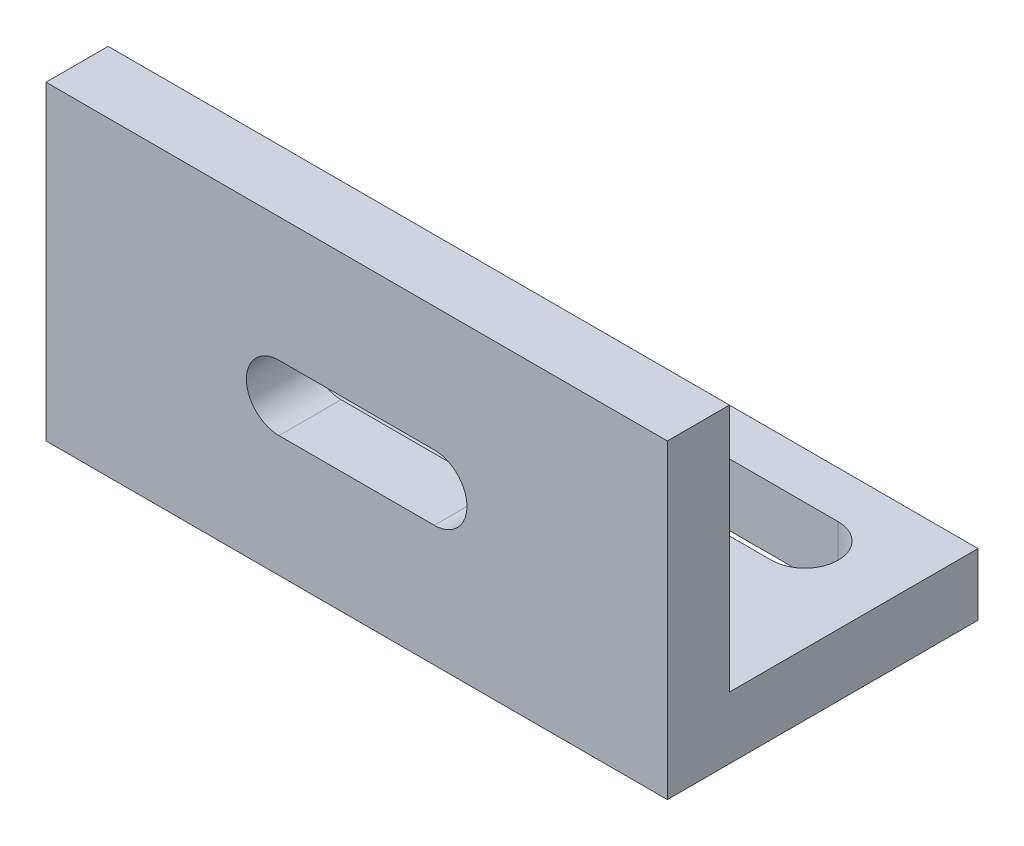
SolidWorks part; units mm, degrees
ref_plane "Front Plane" through (0, 0, 0) normal (0, 0, 1) x (1, 0, 0)
ref_plane "Top Plane" through (0, 0, 0) normal (0, 1, 0) x (1, 0, 0)
ref_plane "Right Plane" through (0, 0, 0) normal (1, 0, 0) x (0, 0, -1)
sketch "Sketch1" plane through (0, 0, 0) normal (0, 1, 0) x (1, 0, 0)
  line L1 (-49.2593, 12.8889) -> (-9.2593, 12.8889)
  line L2 (-49.2593, 12.8889) -> (-49.2593, -7.1111)
  line L4 (-9.2593, 12.8889) -> (-9.2593, -7.1111)
  line L5 (-49.2593, 12.8889) -> (-9.2593, -7.1111) construction
  line L6 (-49.2593, -7.1111) -> (-9.2593, 12.8889) construction
  line L13 (-49.2593, -7.1111) -> (-9.2593, -7.1111)
  line L14 (-49.2593, -7.1111) -> (-49.2593, -3.073)
  line L16 (-9.2593, -7.1111) -> (-9.2593, -3.073)
  point P4 (-29.2593, 2.8889)
  dimension "D1" = 40
  dimension "D2" = 20
extrude "Boss-Extrude1" add sketch "Sketch1" along normal blind 4 contours L2 L13 L4 L1
sketch "Sketch5" plane through (0, 4, 0) normal (0, 1, 0) x (1, 0, 0)
  line L0 (-9.2593, 12.8889) -> (-9.2593, -7.1111) construction
  line L1 (-49.2593, -7.1111) -> (-9.2593, -7.1111)
  line L2 (-49.2593, -7.1111) -> (-49.2593, -3.1111)
  line L3 (-49.2593, -3.1111) -> (-9.2593, -3.1111)
  line L4 (-9.2593, -7.1111) -> (-9.2593, -3.1111)
  line L5 (-49.2593, -7.1111) -> (-9.2593, -3.1111) construction
  line L6 (-49.2593, -3.1111) -> (-9.2593, -7.1111) construction
  point P4 (-29.2593, -5.1111)
  dimension "D1" = 4
extrude "Boss-Extrude2" add sketch "Sketch5" along normal blind 16
sketch "Sketch7" plane through (0, 4, 0) normal (0, 1, 0) x (1, 0, 0)
  line L0 (-49.2593, 12.8889) -> (-9.2593, 12.8889) construction
  line L4 (-15.2593, 7.7389) -> (-43.2593, 7.7389) construction
  line L7 (-15.2593, 5.5889) -> (-43.2593, 5.5889)
  line L8 (-15.2593, 9.8889) -> (-43.2593, 9.8889)
  line L9 (-9.2593, 12.8889) -> (-9.2593, -3.1111) construction
  line L10 (-49.2593, 12.8889) -> (-49.2593, -3.1111) construction
  arc A2 (-15.2593, 5.5889) -> (-15.2593, 9.8889) centre (-15.2593, 7.7389) ccw
  arc A3 (-43.2593, 9.8889) -> (-43.2593, 5.5889) centre (-43.2593, 7.7389) ccw
  point P0 (-29.7561, 8.586)
  point P4 (-29.2593, 12.8889)
  point P8 (-29.2593, 7.7389)
  dimension "D1" = 6
  dimension "D2" = 6
  dimension "D3" = 3
extrude "Cut-Extrude3" cut sketch "Sketch7" against normal blind 10
sketch "Sketch8" plane through (0, 0, 3.1111) normal (0, 0, -1) x (-1, 0, 0)
  line L8 (24.2593, 9.8972) -> (34.2593, 9.8972) construction
  line L9 (24.2593, 11.9972) -> (34.2593, 11.9972)
  line L10 (24.2593, 7.7972) -> (34.2593, 7.7972)
  arc A2 (24.2593, 11.9972) -> (24.2593, 7.7972) centre (24.2593, 9.8972) ccw
  arc A3 (34.2593, 7.7972) -> (34.2593, 11.9972) centre (34.2593, 9.8972) ccw
  point P6 (29.2593, 9.8972)
extrude "Cut-Extrude5" cut sketch "Sketch8" against normal blind 10
